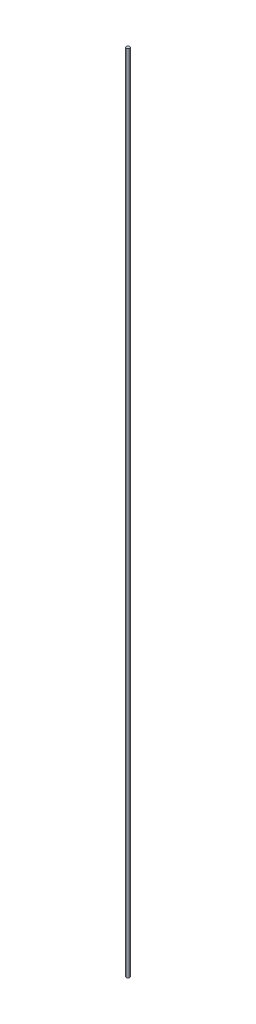
SolidWorks part; units mm, degrees
ref_plane "Front Plane" through (0, 0, 0) normal (0, 0, 1) x (1, 0, 0)
ref_plane "Top Plane" through (0, 0, 0) normal (0, 1, 0) x (1, 0, 0)
ref_plane "Right Plane" through (0, 0, 0) normal (1, 0, 0) x (0, 0, -1)
sketch "Sketch1" plane through (0, 0, 0) normal (0, 1, 0) x (1, 0, 0)
  circle A0 centre (0, 0) radius 2
  dimension "D1" = 4
extrude "Boss-Extrude1" add sketch "Sketch1" along normal blind 1000
